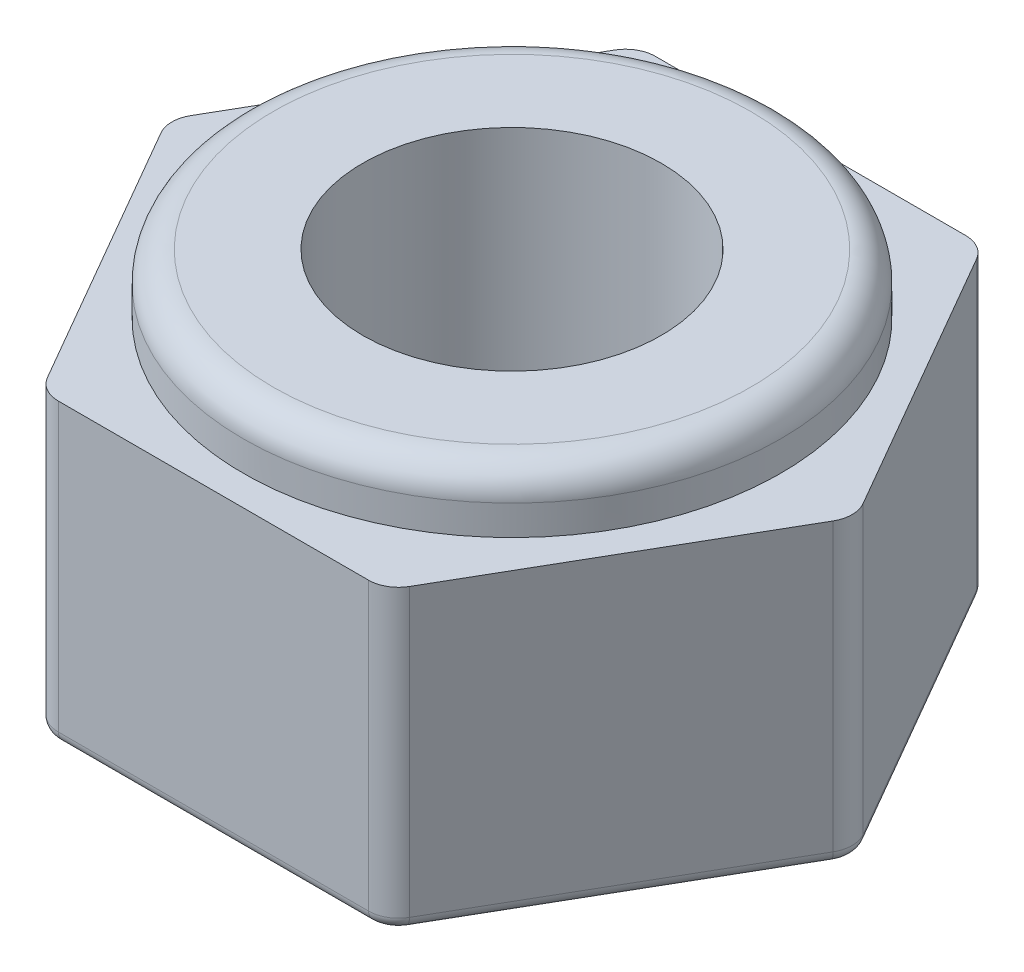
SolidWorks part; units mm, degrees
material "acero"
ref_plane "Alzado" through (0, 0, 0) normal (0, 0, 1) x (1, 0, 0)
ref_plane "Planta" through (0, 0, 0) normal (0, 1, 0) x (1, 0, 0)
ref_plane "Vista lateral" through (0, 0, 0) normal (1, 0, 0) x (0, 0, -1)
sketch "Croquis1" plane through (0, 0, 0) normal (0, 1, 0) x (1, 0, 0)
  line L1 (-2.8868, 5) -> (-5.7735, 0)
  line L2 (-5.7735, 0) -> (-2.8868, -5)
  line L3 (-2.8868, -5) -> (2.8868, -5)
  line L4 (2.8868, -5) -> (5.7735, 0)
  line L5 (5.7735, 0) -> (2.8868, 5)
  line L6 (2.8868, 5) -> (-2.8868, 5)
  circle A0 centre (0, 0) radius 5 construction
  circle A1 centre (0, 0) radius 2.5
  dimension "D1" = 5
  dimension "D2" = 10
extrude "Saliente-Extruir1" add sketch "Croquis1" along normal blind 6
fillet "Redondeo1" radius 0.5 6 edges at (-2.8868, 3, -5) (2.8868, 3, -5) (5.7735, 3, 0) (2.8868, 3, 5) (-5.7735, 3, 0) (-2.8868, 3, 5)
sketch "Croquis2" plane through (0, 6, 0) normal (0, 1, 0) x (1, 0, 0)
  circle A0 centre (0, 0) radius 5.6
  dimension "D1" = 11.2
fillet "Redondeo2" radius 0.2 24 edges at (-2.8481, 0, -4.933) (0, 0, -5) (2.8481, 0, -4.933) (4.3301, 0, -2.5) (5.6962, 0, 0) (4.3301, 0, 2.5) (2.8481, 0, 4.933) (0, 0, 5) (-2.8481, 0, 4.933) (-4.3301, 0, 2.5) (-5.6962, 0, 0) (-2.8481, 6, -4.933) (0, 6, -5) (2.8481, 6, -4.933) (4.3301, 6, -2.5) (5.6962, 6, 0) (4.3301, 6, 2.5) (2.8481, 6, 4.933) (0, 6, 5) (-2.8481, 6, 4.933) (-4.3301, 6, 2.5) (-5.6962, 6, 0) (-4.3301, 0, -2.5) (-4.3301, 6, -2.5)
sketch "Croquis3" plane through (0, 0, 0) normal (0, 0, 1) x (1, 0, 0)
  line L1 (-7, 6) -> (-4.5, 6)
  line L2 (-7, 6) -> (-7, 5)
  line L3 (-7, 5) -> (-4.5, 5)
  line L4 (-4.5, 6) -> (-4.5, 5)
  line L5 (-5.456, 6) -> (-2.8579, 6) construction
  line L7 (0, 0) -> (0, 7.4717) construction
  dimension "D1" = 1
  dimension "D2" = 9
  dimension "D4" = 14
revolve "Cortar-Revolución1" cut sketch "Croquis3" angle 360 about L7
fillet "Redondeo3" radius 0.5 1 edges at (0, 6, -4.5)
